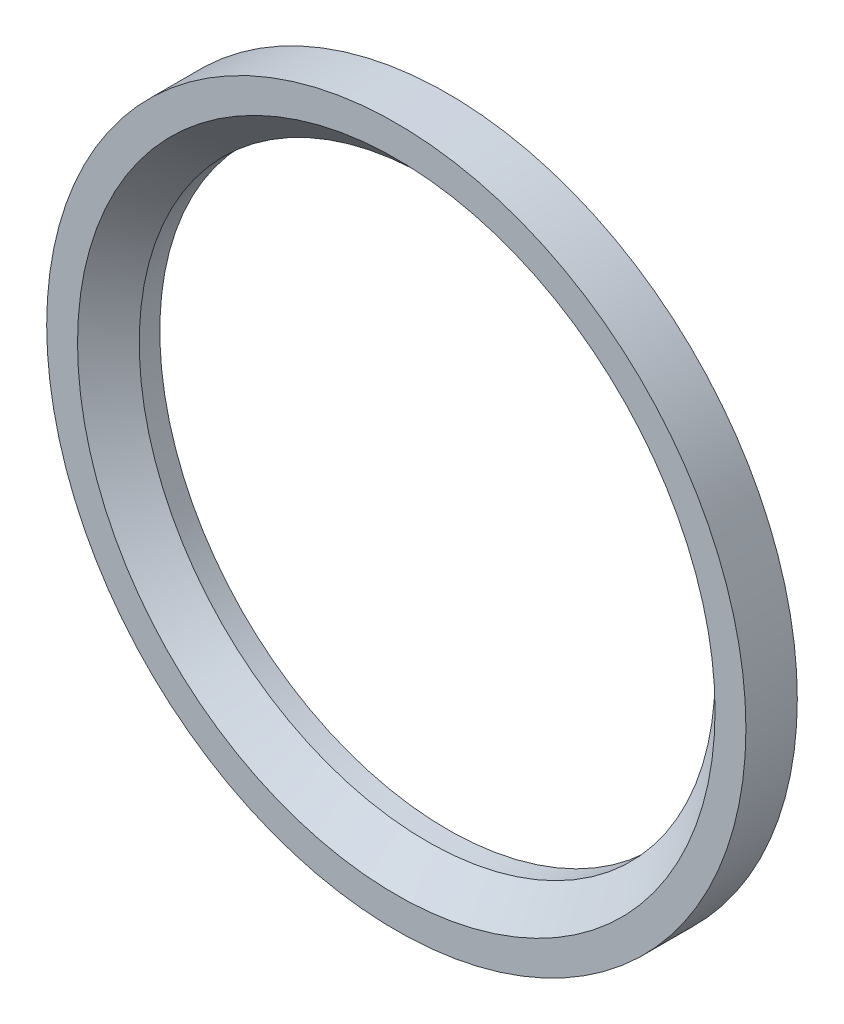
SolidWorks part; units mm, degrees
ref_plane "Front Plane" through (0, 0, 0) normal (0, 0, 1) x (1, 0, 0)
ref_plane "Top Plane" through (0, 0, 0) normal (0, 1, 0) x (1, 0, 0)
ref_plane "Right Plane" through (0, 0, 0) normal (1, 0, 0) x (0, 0, -1)
sketch "Sketch1" plane through (0, 0, 0) normal (0, 0, 1) x (1, 0, 0)
  circle A0 centre (0, 0) radius 14
  circle A1 centre (0, 0) radius 17
  dimension "D1" = 28
  dimension "D2" = 3
extrude "Boss-Extrude1" add sketch "Sketch1" along normal blind 2.5
chamfer "Chamfer1" distance 1.5 angle 45 1 edges at (14, 0, 2.5)
